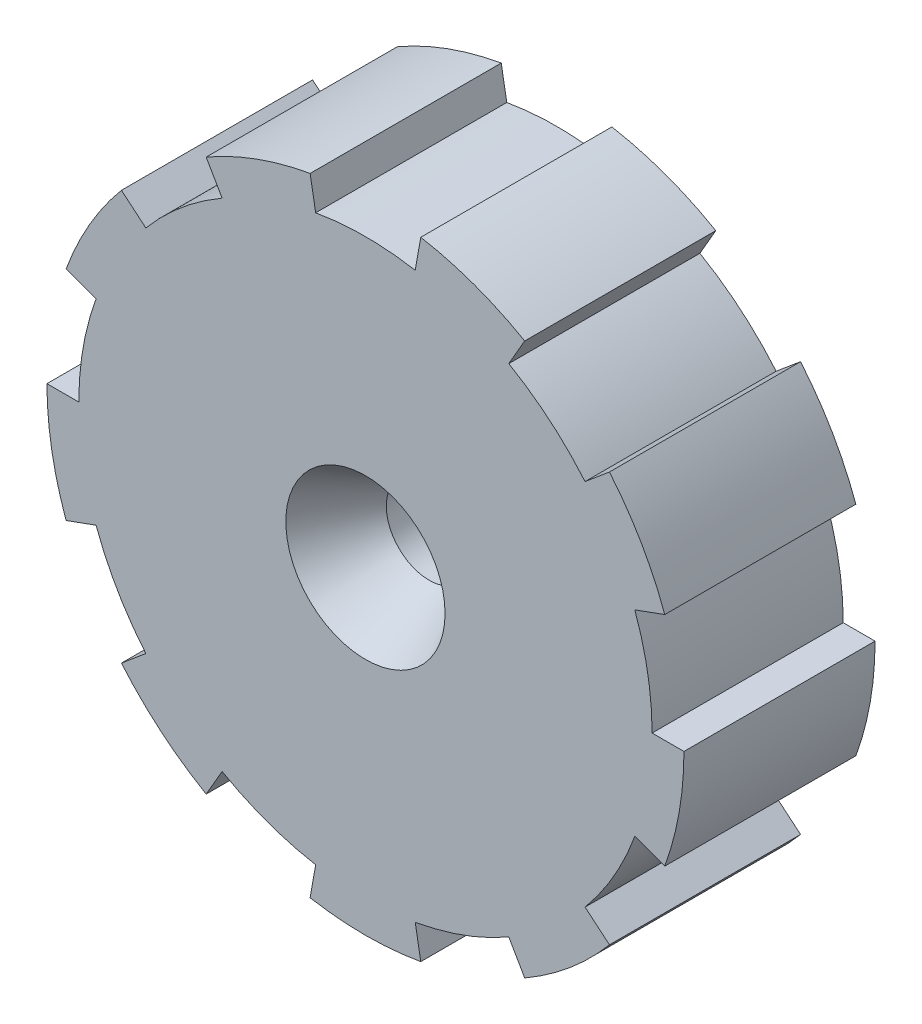
SolidWorks part; units mm, degrees
ref_plane "Front Plane" through (0, 0, 0) normal (0, 0, 1) x (1, 0, 0)
ref_plane "Top Plane" through (0, 0, 0) normal (0, 1, 0) x (1, 0, 0)
ref_plane "Right Plane" through (0, 0, 0) normal (1, 0, 0) x (0, 0, -1)
sketch "Sketch1" plane through (0, 0, 0) normal (0, 0, 1) x (1, 0, 0)
  line L0 (0, 0) -> (0, 50000) construction
  line L1 (-7.8142, 44.3163) -> (-8.6824, 49.2404)
  line L2 (7.8142, 44.3163) -> (8.6824, 49.2404)
  line L3 (34.472, 28.9254) -> (38.3022, 32.1394)
  line L4 (22.5, 38.9711) -> (25, 43.3013)
  line L5 (45, 0) -> (50, 0)
  line L6 (42.2862, 15.3909) -> (46.9846, 17.101)
  line L7 (34.472, -28.9254) -> (38.3022, -32.1394)
  line L8 (42.2862, -15.3909) -> (46.9846, -17.101)
  line L9 (7.8142, -44.3163) -> (8.6824, -49.2404)
  line L10 (22.5, -38.9711) -> (25, -43.3013)
  line L11 (-22.5, -38.9711) -> (-25, -43.3013)
  line L12 (-7.8142, -44.3163) -> (-8.6824, -49.2404)
  line L13 (-42.2862, -15.3909) -> (-46.9846, -17.101)
  line L14 (-34.472, -28.9254) -> (-38.3022, -32.1394)
  line L15 (-42.2862, 15.3909) -> (-46.9846, 17.101)
  line L16 (-45, 0) -> (-50, 0)
  line L17 (-22.5, 38.9711) -> (-25, 43.3013)
  line L18 (-34.472, 28.9254) -> (-38.3022, 32.1394)
  arc A0 (-38.3022, 32.1394) -> (-46.9846, 17.101) centre (0, 0) ccw
  arc A1 (7.8142, 44.3163) -> (-7.8142, 44.3163) centre (0, 0) ccw
  arc A2 (34.472, 28.9254) -> (22.5, 38.9711) centre (0, 0) ccw
  arc A3 (45, 0) -> (42.2862, 15.3909) centre (0, 0) ccw
  arc A4 (34.472, -28.9254) -> (42.2862, -15.3909) centre (0, 0) ccw
  arc A5 (7.8142, -44.3163) -> (22.5, -38.9711) centre (0, 0) ccw
  arc A6 (-22.5, -38.9711) -> (-7.8142, -44.3163) centre (0, 0) ccw
  arc A7 (-42.2862, -15.3909) -> (-34.472, -28.9254) centre (0, 0) ccw
  arc A8 (-42.2862, 15.3909) -> (-45, 0) centre (0, 0) ccw
  arc A9 (-22.5, 38.9711) -> (-34.472, 28.9254) centre (0, 0) ccw
  arc A10 (-50, 0) -> (-46.9846, -17.101) centre (0, 0) ccw
  arc A11 (-38.3022, -32.1394) -> (-25, -43.3013) centre (0, 0) ccw
  arc A12 (-8.6824, -49.2404) -> (8.6824, -49.2404) centre (0, 0) ccw
  arc A13 (25, -43.3013) -> (38.3022, -32.1394) centre (0, 0) ccw
  arc A14 (46.9846, -17.101) -> (50, 0) centre (0, 0) ccw
  arc A15 (46.9846, 17.101) -> (38.3022, 32.1394) centre (0, 0) ccw
  arc A16 (25, 43.3013) -> (8.6824, 49.2404) centre (0, 0) ccw
  arc A17 (-8.6824, 49.2404) -> (-25, 43.3013) centre (0, 0) ccw
  dimension "D1" = 100
  dimension "D3" = 10
  dimension "D2" = 45
  dimension "D4" = 9
extrude "Boss-Extrude1" add sketch "Sketch1" along normal blind 30
sketch "Sketch 2" plane through (0, 0, 30) normal (0, 0, 1) x (1, 0, 0)
  circle A0 centre (0, 0) radius 12.5
  dimension "D1" = 25
extrude "Cut-Extrude1" cut sketch "Sketch 2" against normal blind 10 draft 30
sketch "Sketch3" plane through (0, 0, 0) normal (0, 0, -1) x (-1, 0, 0)
  line L18 (-7.8142, 44.3163) -> (-8.6824, 49.2404)
  line L19 (-25, 43.3013) -> (-22.5, 38.9711)
  line L20 (-34.472, 28.9254) -> (-38.3022, 32.1394)
  line L21 (-46.9846, 17.101) -> (-42.2862, 15.3909)
  line L22 (-45, 0) -> (-50, 0)
  line L23 (-46.9846, -17.101) -> (-42.2862, -15.3909)
  line L24 (-34.472, -28.9254) -> (-38.3022, -32.1394)
  line L25 (-25, -43.3013) -> (-22.5, -38.9711)
  line L26 (-7.8142, -44.3163) -> (-8.6824, -49.2404)
  line L27 (8.6824, -49.2404) -> (7.8142, -44.3163)
  line L28 (22.5, -38.9711) -> (25, -43.3013)
  line L29 (38.3022, -32.1394) -> (34.472, -28.9254)
  line L30 (42.2862, -15.3909) -> (46.9846, -17.101)
  line L31 (50, 0) -> (45, 0)
  line L32 (42.2862, 15.3909) -> (46.9846, 17.101)
  line L33 (38.3022, 32.1394) -> (34.472, 28.9254)
  line L34 (22.5, 38.9711) -> (25, 43.3013)
  line L35 (8.6824, 49.2404) -> (7.8142, 44.3163)
  line L36 (-7.8142, 44.3163) -> (-8.6824, 49.2404)
  line L37 (-25, 43.3013) -> (-22.5, 38.9711)
  line L38 (-34.472, 28.9254) -> (-38.3022, 32.1394)
  line L39 (-46.9846, 17.101) -> (-42.2862, 15.3909)
  line L40 (-45, 0) -> (-50, 0)
  line L41 (-46.9846, -17.101) -> (-42.2862, -15.3909)
  line L42 (-34.472, -28.9254) -> (-38.3022, -32.1394)
  line L43 (-25, -43.3013) -> (-22.5, -38.9711)
  line L44 (-7.8142, -44.3163) -> (-8.6824, -49.2404)
  line L45 (8.6824, -49.2404) -> (7.8142, -44.3163)
  line L46 (22.5, -38.9711) -> (25, -43.3013)
  line L47 (38.3022, -32.1394) -> (34.472, -28.9254)
  line L48 (42.2862, -15.3909) -> (46.9846, -17.101)
  line L49 (50, 0) -> (45, 0)
  line L50 (42.2862, 15.3909) -> (46.9846, 17.101)
  line L51 (38.3022, 32.1394) -> (34.472, 28.9254)
  line L52 (22.5, 38.9711) -> (25, 43.3013)
  line L53 (8.6824, 49.2404) -> (7.8142, 44.3163)
  arc A18 (7.8142, 44.3163) -> (-7.8142, 44.3163) centre (0, 0) ccw
  arc A19 (-8.6824, 49.2404) -> (-25, 43.3013) centre (0, 0) ccw
  arc A20 (-22.5, 38.9711) -> (-34.472, 28.9254) centre (0, 0) ccw
  arc A21 (-38.3022, 32.1394) -> (-46.9846, 17.101) centre (0, 0) ccw
  arc A22 (-42.2862, 15.3909) -> (-45, 0) centre (0, 0) ccw
  arc A23 (-50, 0) -> (-46.9846, -17.101) centre (0, 0) ccw
  arc A24 (-42.2862, -15.3909) -> (-34.472, -28.9254) centre (0, 0) ccw
  arc A25 (-38.3022, -32.1394) -> (-25, -43.3013) centre (0, 0) ccw
  arc A26 (-22.5, -38.9711) -> (-7.8142, -44.3163) centre (0, 0) ccw
  arc A27 (-8.6824, -49.2404) -> (8.6824, -49.2404) centre (0, 0) ccw
  arc A28 (7.8142, -44.3163) -> (22.5, -38.9711) centre (0, 0) ccw
  arc A29 (25, -43.3013) -> (38.3022, -32.1394) centre (0, 0) ccw
  arc A30 (34.472, -28.9254) -> (42.2862, -15.3909) centre (0, 0) ccw
  arc A31 (46.9846, -17.101) -> (50, 0) centre (0, 0) ccw
  arc A32 (45, 0) -> (42.2862, 15.3909) centre (0, 0) ccw
  arc A33 (46.9846, 17.101) -> (38.3022, 32.1394) centre (0, 0) ccw
  arc A34 (34.472, 28.9254) -> (22.5, 38.9711) centre (0, 0) ccw
  arc A35 (25, 43.3013) -> (8.6824, 49.2404) centre (0, 0) ccw
  arc A36 (7.8142, 44.3163) -> (-7.8142, 44.3163) centre (0, 0) ccw
  arc A37 (-8.6824, 49.2404) -> (-25, 43.3013) centre (0, 0) ccw
  arc A38 (-22.5, 38.9711) -> (-34.472, 28.9254) centre (0, 0) ccw
  arc A39 (-38.3022, 32.1394) -> (-46.9846, 17.101) centre (0, 0) ccw
  arc A40 (-42.2862, 15.3909) -> (-45, 0) centre (0, 0) ccw
  arc A41 (-50, 0) -> (-46.9846, -17.101) centre (0, 0) ccw
  arc A42 (-42.2862, -15.3909) -> (-34.472, -28.9254) centre (0, 0) ccw
  arc A43 (-38.3022, -32.1394) -> (-25, -43.3013) centre (0, 0) ccw
  arc A44 (-22.5, -38.9711) -> (-7.8142, -44.3163) centre (0, 0) ccw
  arc A45 (-8.6824, -49.2404) -> (8.6824, -49.2404) centre (0, 0) ccw
  arc A46 (7.8142, -44.3163) -> (22.5, -38.9711) centre (0, 0) ccw
  arc A47 (25, -43.3013) -> (38.3022, -32.1394) centre (0, 0) ccw
  arc A48 (34.472, -28.9254) -> (42.2862, -15.3909) centre (0, 0) ccw
  arc A49 (46.9846, -17.101) -> (50, 0) centre (0, 0) ccw
  arc A50 (45, 0) -> (42.2862, 15.3909) centre (0, 0) ccw
  arc A51 (46.9846, 17.101) -> (38.3022, 32.1394) centre (0, 0) ccw
  arc A52 (34.472, 28.9254) -> (22.5, 38.9711) centre (0, 0) ccw
  arc A53 (25, 43.3013) -> (8.6824, 49.2404) centre (0, 0) ccw
  circle A55 centre (0, 0) radius 12.5 construction
  circle A56 centre (0, 0) radius 12.5
  dimension "D1" = 0
extrude "Cut-Extrude4" cut sketch "Sketch3" against normal blind 10 draft 30 flip side to cut
sketch "Sketch8" plane through (0, 0, 20) normal (0, 0, 1) x (1, 0, 0)
  circle A0 centre (0, 0) radius 6.7265
extrude "Cut-Extrude5" cut sketch "Sketch8" against normal blind 60
